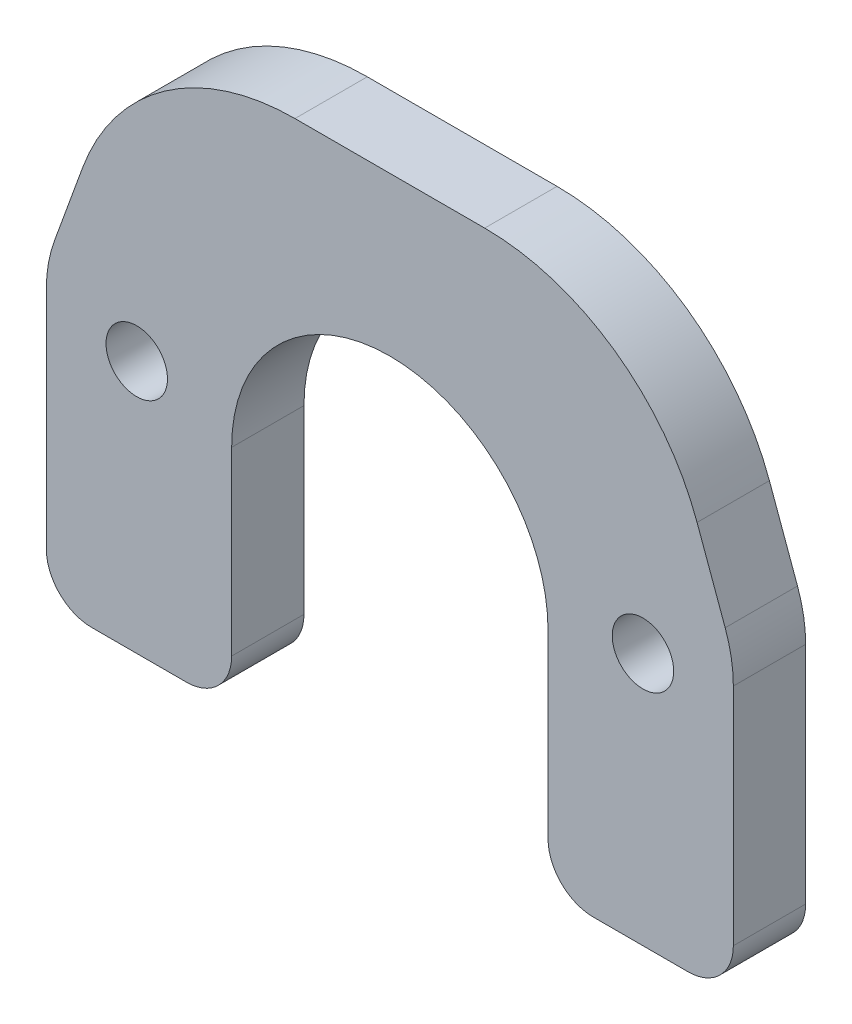
SolidWorks part; units mm, degrees
ref_plane "Plane1" through (0, 0, 0) normal (0, 0, 1) x (1, 0, 0)
ref_plane "Plane2" through (0, 0, 0) normal (0, 1, 0) x (1, 0, 0)
ref_plane "Plane3" through (0, 0, 0) normal (1, 0, 0) x (0, 0, -1)
sketch "Sketch1" plane through (0, 0, 0) normal (0, 0, 1) x (1, 0, 0)
  line L0 (0, 42) -> (0, -53) construction
  line L1 (17.5, -17.5) -> (17.5, -37.5)
  line L2 (-17.5, -17.5) -> (-17.5, -37.5)
  line L3 (22.5, -42.5) -> (33, -42.5)
  line L4 (-22.5, -42.5) -> (-33, -42.5)
  line L5 (38, -37.5) -> (38, -12.6197)
  line L6 (-38, -37.5) -> (-38, -12.6197)
  line L7 (37.0954, -7.4894) -> (33.9871, 1.0505)
  line L8 (-37.0954, -7.4894) -> (-33.9871, 1.0505)
  line L9 (10.4948, 17.5) -> (-10.4948, 17.5)
  arc A0 (-17.5, -17.5) -> (17.5, -17.5) centre (0, -17.5) cw
  arc A1 (37.0954, -7.4894) -> (38, -12.6197) centre (23, -12.6197) cw
  arc A2 (-37.0954, -7.4894) -> (-38, -12.6197) centre (-23, -12.6197) ccw
  arc A3 (-10.4948, 17.5) -> (-33.9871, 1.0505) centre (-10.4948, -7.5) ccw
  arc A4 (10.4948, 17.5) -> (33.9871, 1.0505) centre (10.4948, -7.5) cw
  arc A5 (-22.5, -42.5) -> (-17.5, -37.5) centre (-22.5, -37.5) ccw
  arc A6 (17.5, -37.5) -> (22.5, -42.5) centre (22.5, -37.5) ccw
  arc A7 (38, -37.5) -> (33, -42.5) centre (33, -37.5) cw
  arc A8 (-38, -37.5) -> (-33, -42.5) centre (-33, -37.5) ccw
  point P15 (0, 17.5)
  point P17 (38, -9.9748)
  point P20 (-38, -9.9748)
  point P23 (-28, 17.5)
  point P26 (28, 17.5)
  point P29 (-17.5, -42.5)
  point P32 (17.5, -42.5)
  point P35 (38, -42.5)
  point P38 (-38, -42.5)
  dimension "D1" = 17.5
  dimension "D7" = 5
  dimension "D9" = 15
  dimension "D8" = 25
  dimension "D2" = 25
  dimension "D3" = 60
  dimension "D4" = 56
  dimension "D5" = 76
  dimension "D10" = 20
extrude "Base-Extrude" add sketch "Sketch1" along normal blind 8
sketch "Sketch4" plane through (0, 0, 8) normal (0, 0, 1) x (1, 0, 0)
  line L0 (-28, -14.5) -> (28, -14.5) construction
  line L1 (0, 30) -> (0, -43) construction
  line L2 (-22.5, -42.5) -> (-33, -42.5) construction
  circle A0 centre (-28, -14.5) radius 3.4
  circle A1 centre (28, -14.5) radius 3.4
  dimension "D1" = 6.8
  dimension "D3" = 56
  dimension "D2" = 28
extrude "M8 gevindhuller" cut sketch "Sketch4" against normal blind 10
cosmetic thread "Cosmetic Thread1" parameters "D2"=8
cosmetic thread "Cosmetic Thread2" parameters "D2"=8
